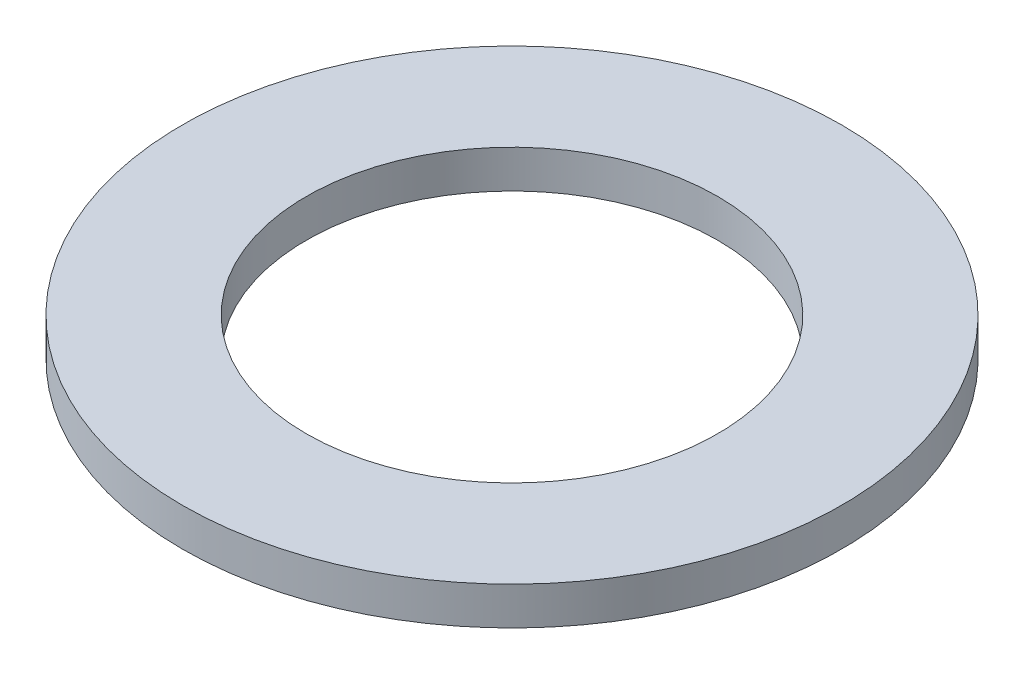
SolidWorks part; units mm, degrees
ref_plane "Front Plane" through (0, 0, 0) normal (0, 0, 1) x (1, 0, 0)
ref_plane "Top Plane" through (0, 0, 0) normal (0, 1, 0) x (1, 0, 0)
ref_plane "Right Plane" through (0, 0, 0) normal (1, 0, 0) x (0, 0, -1)
sketch "Sketch1" plane through (0, 0, 0) normal (0, 1, 0) x (1, 0, 0)
  circle A0 centre (0, 0) radius 7.9375
  dimension "OD" = 15.875
extrude "Boss-Extrude1" add sketch "Sketch1" along normal blind 0.9144
sketch "Sketch5" plane through (0, 0.9144, 0) normal (0, 1, 0) x (-1, 0, 0)
  circle A0 centre (0, 0) radius 4.953
  dimension "ID" = 9.906
extrude "Cut-Extrude1" cut sketch "Sketch5" against normal through all
